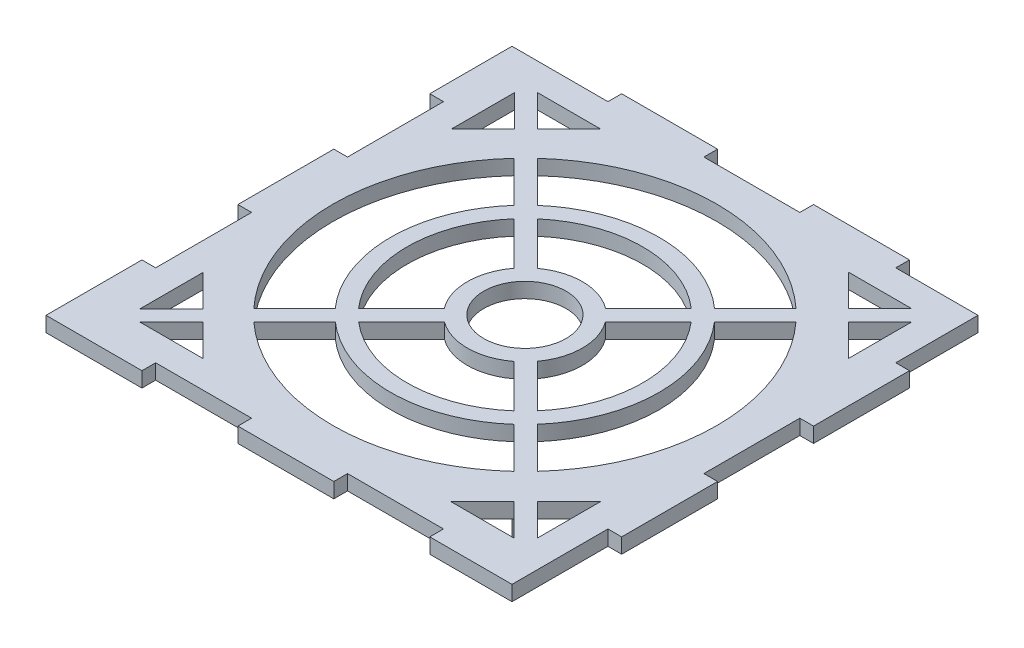
SolidWorks part; units mm, degrees
ref_plane "Спереди" through (0, 0, 0) normal (0, 0, 1) x (1, 0, 0)
ref_plane "Сверху" through (0, 0, 0) normal (0, 1, 0) x (1, 0, 0)
ref_plane "Справа" through (0, 0, 0) normal (1, 0, 0) x (0, 0, -1)
other "Configuration Table"
sketch "Эскиз1" plane through (0, 0, 0) normal (0, 1, 0) x (1, 0, 0)
  line L5 (0, 0) -> (175, 0)
  line L6 (0, 0) -> (0, 175)
  line L7 (0, 175) -> (175, 175)
  line L8 (175, 0) -> (175, 175)
  line L23 (175, 0) -> (169.5, 0)
  line L24 (175, 0) -> (175, 28.3)
  line L28 (175, 58.35) -> (175, 86.65)
  line L32 (175, 116.7) -> (175, 145)
  line L34 (0, 175) -> (35, 175)
  line L35 (0, 175) -> (0, 170)
  line L36 (0, 175) -> (28.3333, 175)
  line L37 (0, 175) -> (0, 170)
  line L40 (58.35, 175) -> (86.6833, 175)
  line L44 (116.7, 175) -> (145.0333, 175)
  line L48 (116.7, 0) -> (145.0333, 0)
  line L52 (58.35, 0) -> (86.6833, 0)
  line L58 (0, 0) -> (28.3333, 0)
  line L59 (0, 0) -> (0, 5)
  line L63 (175, 0) -> (169.5, 0)
  line L74 (-24.5534, -24.5534) -> (199.6635, 199.6635) construction
  line L75 (-26.6748, -22.4321) -> (197.5421, 201.7848)
  line L76 (-22.4321, -26.6748) -> (201.7848, 197.5421)
  line L77 (-26.6748, 201.6748) -> (199.6635, -24.6635) construction
  line L78 (-24.5534, 203.7961) -> (201.7848, -22.5421)
  line L79 (-28.7961, 199.5534) -> (197.5421, -26.7848)
  line L80 (160.0128, 155.7702) -> (160.0128, 132.7432)
  line L81 (160.0128, 132.7432) -> (148.4993, 144.2567)
  line L82 (148.4993, 144.2567) -> (160.0128, 155.7702)
  line L83 (132.7432, 160.0128) -> (144.2567, 148.4993)
  line L84 (155.7702, 160.0128) -> (132.7432, 160.0128)
  line L85 (144.2567, 148.4993) -> (155.7702, 160.0128)
  line L86 (0, 0) -> (5, 0)
  line L87 (15.0972, 132.7432) -> (26.6107, 144.2567)
  line L88 (15.0972, 155.7702) -> (15.0972, 132.7432)
  line L89 (26.6107, 144.2567) -> (15.0972, 155.7702)
  line L90 (19.3398, 160.0128) -> (42.3668, 160.0128)
  line L91 (30.8533, 148.4993) -> (19.3398, 160.0128)
  line L92 (42.3668, 160.0128) -> (30.8533, 148.4993)
  line L93 (155.7702, 14.9872) -> (132.7432, 14.9872)
  line L94 (144.2567, 26.5007) -> (155.7702, 14.9872)
  line L95 (132.7432, 14.9872) -> (144.2567, 26.5007)
  line L96 (160.0128, 42.2568) -> (148.4993, 30.7433)
  line L97 (160.0128, 19.2298) -> (160.0128, 42.2568)
  line L98 (148.4993, 30.7433) -> (160.0128, 19.2298)
  line L99 (30.8533, 26.5007) -> (19.3398, 14.9872)
  line L100 (42.3668, 14.9872) -> (30.8533, 26.5007)
  line L101 (19.3398, 14.9872) -> (42.3668, 14.9872)
  line L102 (15.0972, 19.2298) -> (15.0972, 42.2568)
  line L103 (26.6107, 30.7433) -> (15.0972, 19.2298)
  line L104 (15.0972, 42.2568) -> (26.6107, 30.7433)
  line L105 (0, 0) -> (0, 5)
  line L108 (175, 0) -> (175, 5.5)
  line L111 (70, 175) -> (70, 170)
  line L112 (0, 175) -> (35, 175)
  line L113 (0, 175) -> (0, 170)
  line L114 (0, 170) -> (35, 170)
  line L115 (35, 175) -> (35, 170)
  line L116 (70, 175) -> (105, 175)
  line L117 (105, 175) -> (105, 170)
  line L124 (0, 0) -> (35, 0)
  line L125 (0, 0) -> (0, 5)
  line L127 (35, 0) -> (35, 5)
  line L128 (70.1, 0) -> (104.9, 0)
  line L132 (140.1, 0) -> (175, 0)
  line L133 (175, 0) -> (175, 5.5)
  line L135 (70, 5) -> (35, 5)
  line L136 (70, 0) -> (70, 5)
  line L138 (70, 170) -> (105, 170)
  line L150 (0, 70.1) -> (0, 104.9)
  line L151 (0, 0) -> (5, 0)
  line L152 (0, 0) -> (0, 35)
  line L158 (0, 140.1) -> (0, 175)
  line L161 (0, 175) -> (5.5, 175)
  line L162 (0, 70) -> (0, 105)
  line L163 (0, 70) -> (5, 70)
  line L164 (140, 175) -> (140, 170)
  line L165 (140, 175) -> (175, 175)
  line L166 (175, 175) -> (175, 170)
  line L167 (140, 170) -> (175, 170)
  line L168 (175, 105) -> (175, 70)
  line L169 (175, 175) -> (170, 175)
  line L170 (175, 175) -> (175, 140)
  line L171 (175, 140) -> (170, 140)
  line L172 (170, 175) -> (170, 140)
  line L173 (175, 105) -> (170, 105)
  line L174 (170, 105) -> (170, 70)
  line L175 (175, 70) -> (170, 70)
  line L176 (175, 35) -> (175, 0)
  line L177 (175, 35) -> (170, 35)
  line L178 (170, 35) -> (170, 0)
  line L179 (175, 0) -> (170, 0)
  line L180 (0, 0) -> (35, 0)
  line L181 (0, 0) -> (0, 5)
  line L183 (35, 0) -> (35, 5)
  line L184 (70, 0) -> (105, 0)
  line L185 (105, 0) -> (105, 5)
  line L187 (140, 0) -> (140, 5)
  line L188 (140, 0) -> (175, 0)
  line L189 (175, 0) -> (175, 5)
  line L191 (105, 5) -> (140, 5)
  line L192 (0, 0) -> (5, 0)
  line L195 (0, 0) -> (0, 35)
  line L196 (0, 35) -> (5, 35)
  line L199 (0, 105) -> (5, 105)
  line L200 (0, 140) -> (0, 175)
  line L201 (0, 140) -> (5, 140)
  line L203 (0, 175) -> (5, 175)
  line L204 (5, 140) -> (5, 105)
  line L205 (5, 35) -> (5, 70)
  circle A0 centre (87.2046, 87.5) radius 15
  circle A1 centre (87.2046, 87.5) radius 21
  circle A2 centre (87.2046, 87.5) radius 43
  circle A3 centre (87.2046, 87.5) radius 49
  circle A5 centre (87.2046, 87.5) radius 70
  arc A7 (-26.6748, -22.4321) -> (-22.4321, -26.6748) centre (-24.5534, -24.5534) ccw
  arc A8 (201.7848, 197.5421) -> (197.5421, 201.7848) centre (199.6635, 199.6635) ccw
  arc A9 (-24.5534, 203.7961) -> (-28.7961, 199.5534) centre (-26.6748, 201.6748) ccw
  arc A10 (197.5421, -26.7848) -> (201.7848, -22.5421) centre (199.6635, -24.6635) ccw
  point P33 (0, 0)
  point P55 (87.2046, 87.5)
  point P65 (87.555, 87.555)
  point P72 (86.4943, 88.5057)
  point P85 (87.2046, 87.5)
  dimension "D3" = 3
  dimension "D1" = 3
  dimension "D4" = 3
  dimension "D2" = 3
extrude "Бобышка-Вытянуть2" add sketch "Эскиз1" along normal blind 5.5
sketch "Эскиз2" plane through (0, 5.5, 0) normal (0, 1, 0) x (1, 0, 0)
  line L0 (30.8533, 148.4993) -> (26.6107, 144.2567)
  line L1 (30.8533, 148.4993) -> (35.8111, 143.5415)
  line L2 (26.6107, 144.2567) -> (31.5685, 139.2989)
  line L3 (35.8111, 143.5415) -> (31.5685, 139.2989)
  line L4 (148.2039, 143.8513) -> (143.9613, 148.0939)
  line L5 (148.2039, 143.8513) -> (143.2461, 138.8935)
  line L6 (143.2461, 138.8935) -> (139.0035, 143.1361)
  line L7 (143.9613, 148.0939) -> (139.0035, 143.1361)
  line L8 (143.5558, 26.5007) -> (147.7985, 30.7433)
  line L9 (143.5558, 26.5007) -> (138.5981, 31.4585)
  line L10 (138.5981, 31.4585) -> (142.8407, 35.7011)
  line L11 (147.7985, 30.7433) -> (142.8407, 35.7011)
  line L12 (26.2053, 31.1487) -> (30.4479, 26.9061)
  line L13 (26.2053, 31.1487) -> (31.1631, 36.1065)
  line L14 (31.1631, 36.1065) -> (35.4057, 31.8639)
  line L15 (30.4479, 26.9061) -> (35.4057, 31.8639)
  line L16 (87.2046, 87.5) -> (31.5685, 139.2989) construction
  dimension "D2" = 76.0165
  dimension "D1" = 4
extrude "Бобышка-Вытянуть3" add sketch "Эскиз2" against normal blind 23
